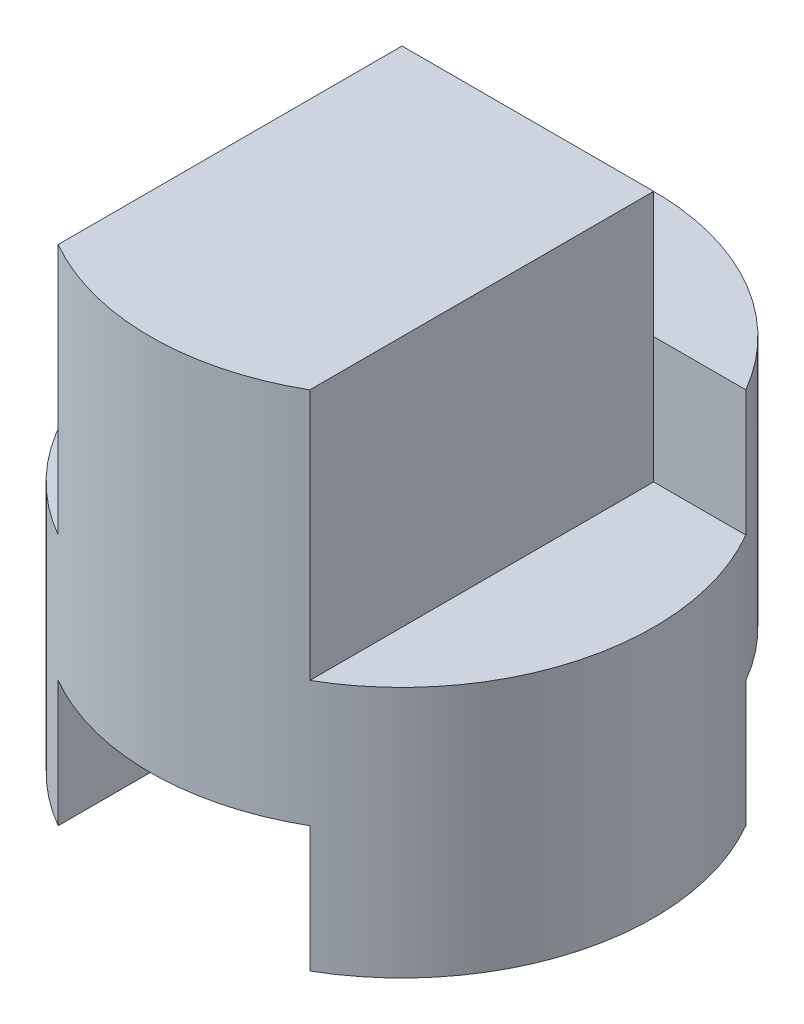
SolidWorks part; units mm, degrees
ref_plane "Front" through (0, 0, 0) normal (0, 0, 1) x (1, 0, 0)
ref_plane "Top" through (0, 0, 0) normal (0, 1, 0) x (1, 0, 0)
ref_plane "Right" through (0, 0, 0) normal (1, 0, 0) x (0, 0, -1)
sketch "Sketch1" plane through (0, 0, 0) normal (0, 1, 0) x (1, 0, 0)
  circle A0 centre (0, 0) radius 2
  dimension "D1" = 4
extrude "Boss-Extrude1" add sketch "Sketch1" along normal blind 4
sketch "Sketch2" plane through (0, 0, 0) normal (0, 0, 1) x (1, 0, 0)
  line L0 (-1, 1) -> (1, 1)
  line L4 (-1, 0) -> (-1, 1)
  line L16 (1, 0) -> (1, 1)
  line L17 (1, 0) -> (-1, 0)
  dimension "D4" = 1
extrude "Cut-Extrude1" cut sketch "Sketch2" against normal mid plane 4
sketch "Sketch3" plane through (0, 0, 0) normal (0, 0, 1) x (1, 0, 0)
  line L1 (2, 4) -> (2, 3)
  line L2 (2, 0) -> (2, 4) construction
  line L7 (-1, 2) -> (-2, 2)
  line L8 (-2, 4) -> (-2, 0) construction
  line L9 (-2, 2) -> (-2, 4)
  line L10 (-1, 2) -> (-1, 3)
  line L13 (0.9998, 3) -> (0.9998, 2)
  line L14 (0.9998, 2) -> (2, 2)
  line L15 (2, 0) -> (2, 4) construction
  line L16 (2, 2) -> (2, 3)
  line L17 (-1, 3) -> (-1, 4)
  line L18 (-1, 4) -> (-2, 4)
  line L19 (0.9998, 3) -> (0.9998, 4)
  line L20 (0.9998, 4) -> (2, 4)
  dimension "D1" = 2
  dimension "D2" = 1
extrude "Cut-Extrude2" cut sketch "Sketch3" against normal blind 1 and the other way blind 4
sketch "Sketch4" plane through (0, 4, 0) normal (0, 1, 0) x (1, 0, 0)
  line L0 (-1.7321, 1) -> (1.7321, 1)
  arc A0 (-1.7321, 1) -> (1.7321, 1) centre (0, 0) cw
extrude "Cut-Extrude3" cut sketch "Sketch4" against normal blind 1
sketch "Sketch5" plane through (0, 0, 0) normal (0, -1, 0) x (1, 0, 0)
  line L0 (-1.7321, -1) -> (1.7321, -1)
  arc A0 (-1.7321, -1) -> (1.7321, -1) centre (0, 0) ccw
extrude "Cut-Extrude4" cut sketch "Sketch5" against normal blind 1
